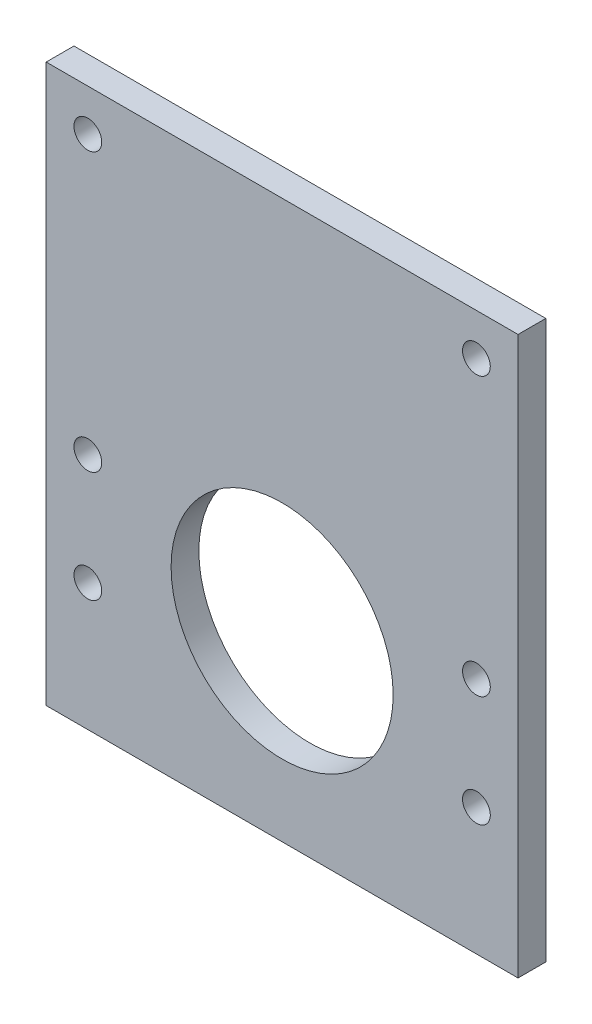
SolidWorks part; units mm, degrees
ref_plane "Front Plane" through (0, 0, 0) normal (0, 0, 1) x (1, 0, 0)
ref_plane "Top Plane" through (0, 0, 0) normal (0, 1, 0) x (1, 0, 0)
ref_plane "Right Plane" through (0, 0, 0) normal (1, 0, 0) x (0, 0, -1)
sketch "Sketch1" plane through (0, 0, 0) normal (0, 0, 1) x (1, 0, 0)
  line L0 (-44.45, 76.2) -> (-44.45, -32.258) construction
  line L1 (-53.975, 85.725) -> (53.975, 85.725)
  line L2 (-53.975, 85.725) -> (-53.975, -41.783)
  line L3 (-53.975, -41.783) -> (53.975, -41.783)
  line L4 (53.975, 85.725) -> (53.975, -41.783)
  line L5 (-44.45, -32.258) -> (44.45, -32.258) construction
  line L6 (44.45, 76.2) -> (44.45, -32.258) construction
  line L7 (-44.45, 76.2) -> (44.45, 76.2) construction
  line L8 (0, -41.783) -> (0, 85.725) construction
  circle A0 centre (0, 0) radius 25.4
  circle A1 centre (-44.45, 76.2) radius 3.175
  circle A2 centre (44.45, 76.2) radius 3.175
  circle A3 centre (-44.45, 12.7) radius 3.175
  circle A4 centre (-44.45, -12.7) radius 3.175
  circle A5 centre (44.45, -12.7) radius 3.175
  circle A6 centre (44.45, 12.7) radius 3.175
  point P8 (0, 85.725)
  dimension "D1" = 50.8
  dimension "D5" = 6.35
  dimension "D6" = 25.4
  dimension "D2" = 107.95
  dimension "D3" = 127.508
  dimension "D7" = 88.9
  dimension "D8" = 12.7
  dimension "D4" = 9.525
extrude "Boss-Extrude1" add sketch "Sketch1" along normal blind 6.35
